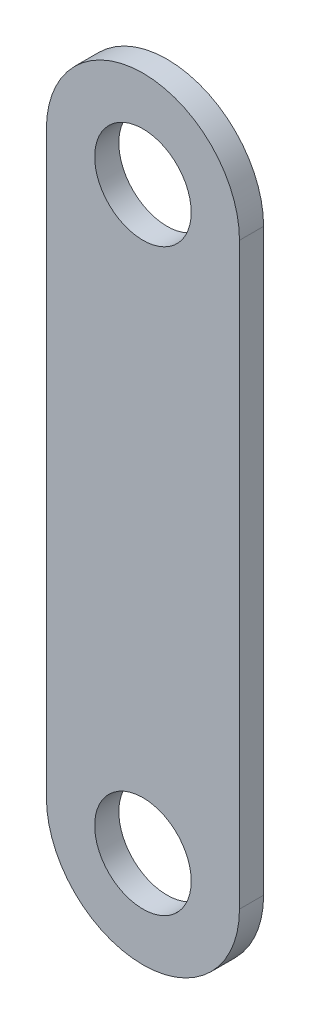
SolidWorks part; units mm, degrees
ref_plane "Front" through (0, 0, 0) normal (0, 0, 1) x (1, 0, 0)
ref_plane "Top" through (0, 0, 0) normal (0, 1, 0) x (1, 0, 0)
ref_plane "Right" through (0, 0, 0) normal (1, 0, 0) x (0, 0, -1)
sketch "Sketch1" plane through (0, 0, 0) normal (0, 0, 1) x (1, 0, 0)
  line L1 (-23.7341, 33.1296) -> (1.6659, 33.1296)
  line L2 (-23.7341, 33.1296) -> (-23.7341, -43.0704)
  line L3 (-23.7341, -43.0704) -> (1.6659, -43.0704)
  line L4 (1.6659, 33.1296) -> (1.6659, -43.0704)
  circle A0 centre (-11.0341, 33.1296) radius 12.7
  circle A1 centre (-11.0341, -43.0704) radius 12.7
  circle A2 centre (-11.0341, 33.1296) radius 6.35
  circle A3 centre (-11.0341, -43.0704) radius 6.35
  dimension "D1" = 12.7
  dimension "D2" = 12.7
  dimension "D3" = 25.4
  dimension "D5" = 25.4
  dimension "D4" = 25.4
  dimension "D6" = 76.2
extrude "Boss-Extrude1" add sketch "Sketch1" along normal blind 3.175 contours A1 L4 A0 L2 | A2 L1 A0 | A2 L1 A0 | A3 L3 A1 | A3 L3 A1 | A1 A0 L2
